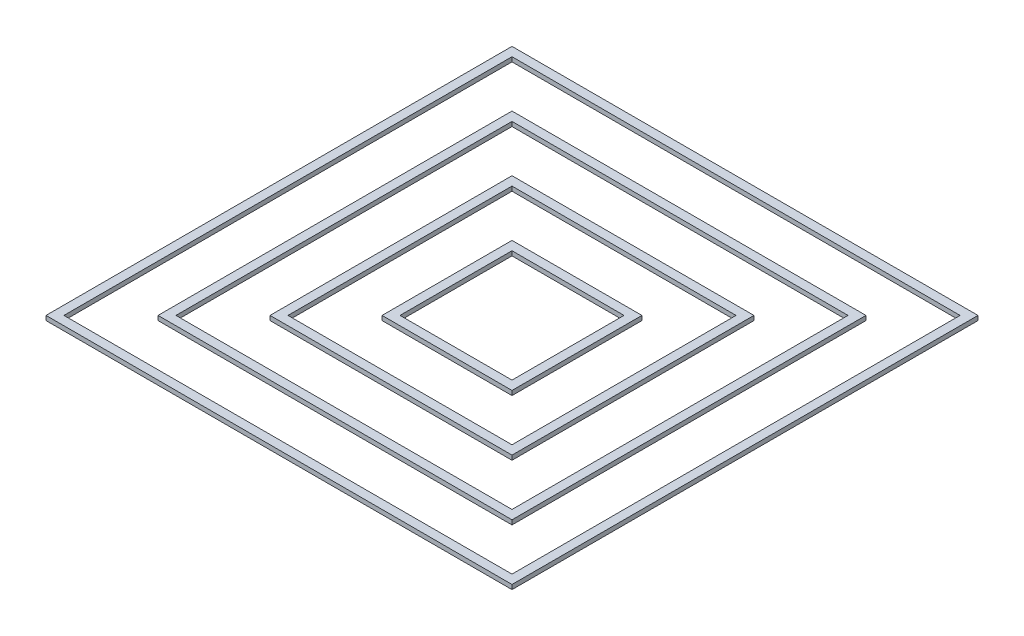
SolidWorks part; units mm, degrees
ref_plane "Front Plane" through (0, 0, 0) normal (0, 0, 1) x (1, 0, 0)
ref_plane "Top Plane" through (0, 0, 0) normal (0, 1, 0) x (1, 0, 0)
ref_plane "Right Plane" through (0, 0, 0) normal (1, 0, 0) x (0, 0, -1)
sketch "Sketch1" plane through (0, 0, 0) normal (0, 1, 0) x (1, 0, 0)
  line L1 (-85.8676, 59.5707) -> (114.1324, 59.5707)
  line L2 (-85.8676, 59.5707) -> (-85.8676, -140.4293)
  line L3 (-85.8676, -140.4293) -> (114.1324, -140.4293)
  line L4 (114.1324, 59.5707) -> (114.1324, -140.4293)
  line L5 (-60.8676, 34.5707) -> (89.1324, 34.5707)
  line L6 (-60.8676, 34.5707) -> (-60.8676, -115.4293)
  line L7 (-60.8676, -115.4293) -> (89.1324, -115.4293)
  line L8 (89.1324, 34.5707) -> (89.1324, -115.4293)
  line L9 (-35.8676, 9.5707) -> (64.1324, 9.5707)
  line L10 (-35.8676, 9.5707) -> (-35.8676, -90.4293)
  line L11 (-35.8676, -90.4293) -> (64.1324, -90.4293)
  line L12 (64.1324, 9.5707) -> (64.1324, -90.4293)
  line L13 (-10.8676, -15.4293) -> (39.1324, -15.4293)
  line L14 (-10.8676, -15.4293) -> (-10.8676, -65.4293)
  line L15 (-10.8676, -65.4293) -> (39.1324, -65.4293)
  line L16 (39.1324, -15.4293) -> (39.1324, -65.4293)
  dimension "D1" = 200
  dimension "D2" = 200
  dimension "D3" = 150
  dimension "D4" = 100
  dimension "D5" = 100
  dimension "D6" = 150
  dimension "D7" = 25
  dimension "D8" = 25
  dimension "D9" = 25
  dimension "D10" = 25
  dimension "D11" = 50
  dimension "D12" = 50
  dimension "D13" = 25
  dimension "D14" = 25
extrude "Extrude-Thin1" add sketch "Sketch1" along normal blind 2 thin contours L3 L4 L1 L2 | L7 L8 L5 L6 | L11 L12 L9 L10 | L15 L16 L13 L14 thin type one direction wall 4
